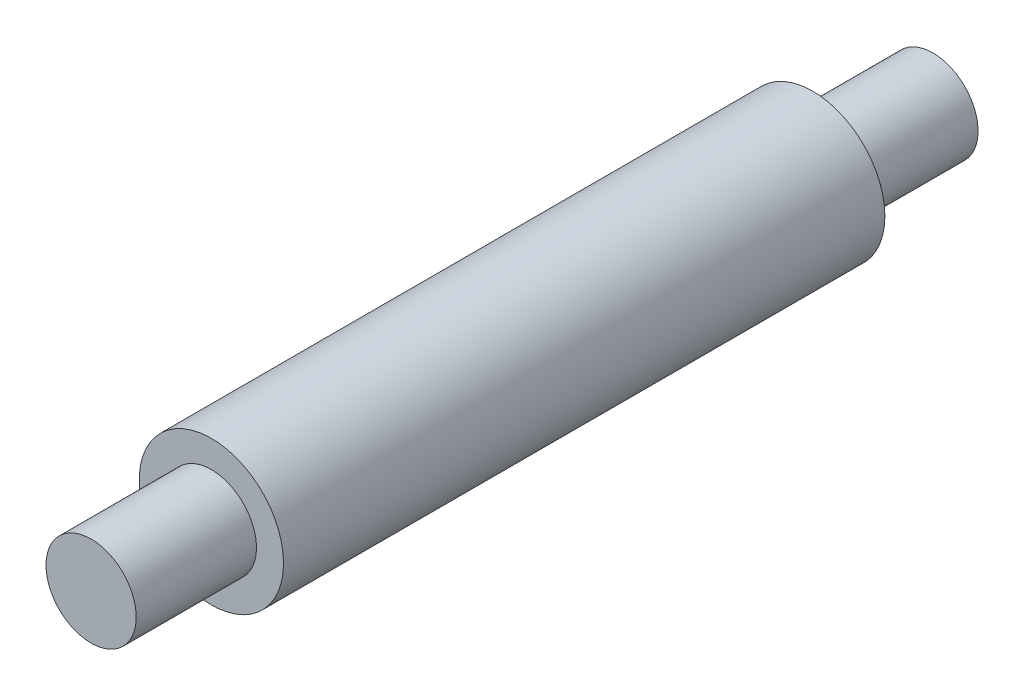
SolidWorks part; units mm, degrees
ref_plane "Front Plane" through (0, 0, 0) normal (0, 0, 1) x (1, 0, 0)
ref_plane "Top Plane" through (0, 0, 0) normal (0, 1, 0) x (1, 0, 0)
ref_plane "Right Plane" through (0, 0, 0) normal (1, 0, 0) x (0, 0, -1)
sketch "Sketch1" plane through (0, 0, 0) normal (0, 0, 1) x (1, 0, 0)
  circle A0 centre (0, 0) radius 24
  dimension "D1" = 48
extrude "Boss-Extrude1" add sketch "Sketch1" along normal blind 200
sketch "Sketch2" plane through (0, 0, 0) normal (0, 0, -1) x (-1, 0, 0)
  circle A0 centre (0, 0) radius 15
  dimension "D1" = 30
extrude "Boss-Extrude2" add sketch "Sketch2" along normal blind 40 contours A0
pattern_linear "LPattern1" count 2 spacing 240 along (0, 0, 1) of "Boss-Extrude2"
